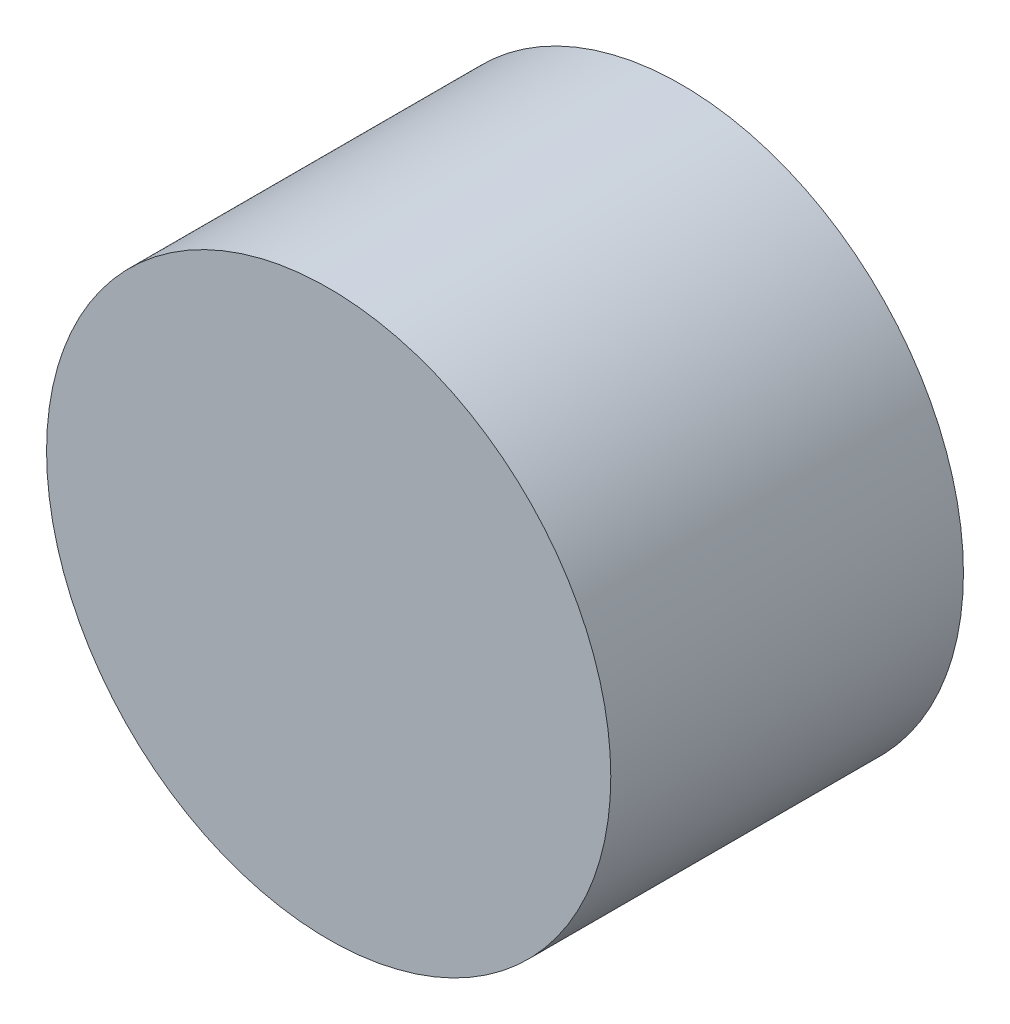
SolidWorks part; units mm, degrees
material "ABS"
ref_plane "Front Plane" through (0, 0, 0) normal (0, 0, 1) x (1, 0, 0)
ref_plane "Top Plane" through (0, 0, 0) normal (0, 1, 0) x (1, 0, 0)
ref_plane "Right Plane" through (0, 0, 0) normal (1, 0, 0) x (0, 0, -1)
sketch "Sketch2" plane through (0, 0, 0) normal (0, 0, 1) x (1, 0, 0)
  arc A0 (-250, 67.5) -> (-250, 107.5) centre (-250, 87.5) ccw construction
  arc A1 (-250, 107.5) -> (-250, 67.5) centre (-250, 87.5) ccw construction
  arc A2 (-250, 67.5) -> (-250, 107.5) centre (-250, 87.5) ccw
  arc A3 (-250, 107.5) -> (-250, 67.5) centre (-250, 87.5) ccw
extrude "Boss-Extrude1" add sketch "Sketch2" along normal blind 25
